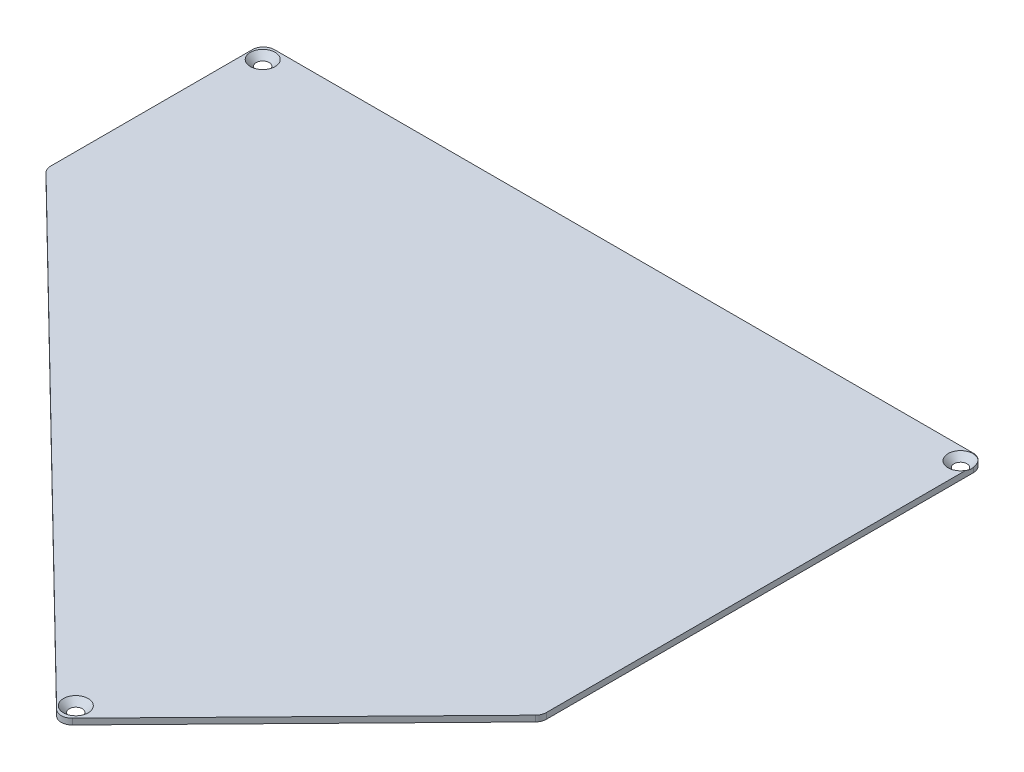
SolidWorks part; units mm, degrees
ref_plane "Front Plane" through (0, 0, 0) normal (0, 0, 1) x (1, 0, 0)
ref_plane "Top Plane" through (0, 0, 0) normal (0, 1, 0) x (1, 0, 0)
ref_plane "Right Plane" through (0, 0, 0) normal (1, 0, 0) x (0, 0, -1)
sketch "Sketch1" plane through (0, 0, 0) normal (0, 1, 0) x (1, 0, 0)
  line L5 (85.0238, -74.3812) -> (143.2252, -14.8361)
  line L6 (144.0228, -12.8789) -> (144.0228, 95.7042)
  line L7 (141.2228, 98.5042) -> (-36.4912, 98.5042)
  line L8 (-39.2912, 95.7042) -> (-39.2912, 44.3918)
  line L9 (-38.4484, 42.3894) -> (81.0643, -74.4264)
  arc A5 (143.2252, -14.8361) -> (144.0228, -12.8789) centre (141.2228, -12.8789) ccw
  arc A6 (144.0228, 95.7042) -> (141.2228, 98.5042) centre (141.2228, 95.7042) ccw
  arc A7 (-36.4912, 98.5042) -> (-39.2912, 95.7042) centre (-36.4912, 95.7042) ccw
  arc A8 (-39.2912, 44.3918) -> (-38.4484, 42.3894) centre (-36.4912, 44.3918) ccw
  arc A9 (81.0643, -74.4264) -> (85.0238, -74.3812) centre (83.0215, -72.424) ccw
extrude "Boss-Extrude2" add sketch "Sketch1" along normal blind 1.5
hole_wizard "CSK for M3 Flat Head Machine Screw1" positions "Sketch2" profile "Sketch3" countersink size "M3" standard "ANSI Metric" end condition up to next
sketch "Sketch2" plane through (0, 1.5, 0) normal (0, 1, 0) x (1, 0, 0)
  point P0 (-35.8105, 94.8501)
  point P3 (141.2294, 95.2042)
  point P6 (82.7039, -71.1881)
sketch "Sketch3" plane through (-35.8105, 1.5, -94.8501) normal (1, 0, 0) x (0, 0, 1)
  line L0 (0, 0) -> (0, 1.5)
  line L1 (0, 1.5) -> (1.6, 1.5)
  line L2 (1.6, 1.5) -> (1.6, 1.55)
  line L3 (1.6, 1.55) -> (3.15, 0)
  line L5 (3.15, 0) -> (0, 0)
  line L6 (-1.6, 1.55) -> (-3.15, 0) construction
  line L11 (0, -6.35) -> (0, 107.95) construction
  dimension "Thru Hole Dia." = 3.2
  dimension "Thru Hole Depth" = 1.5
  dimension "Near C'Sink Dia." = 6.3
  dimension "Near C'Sink Angle" = 90
